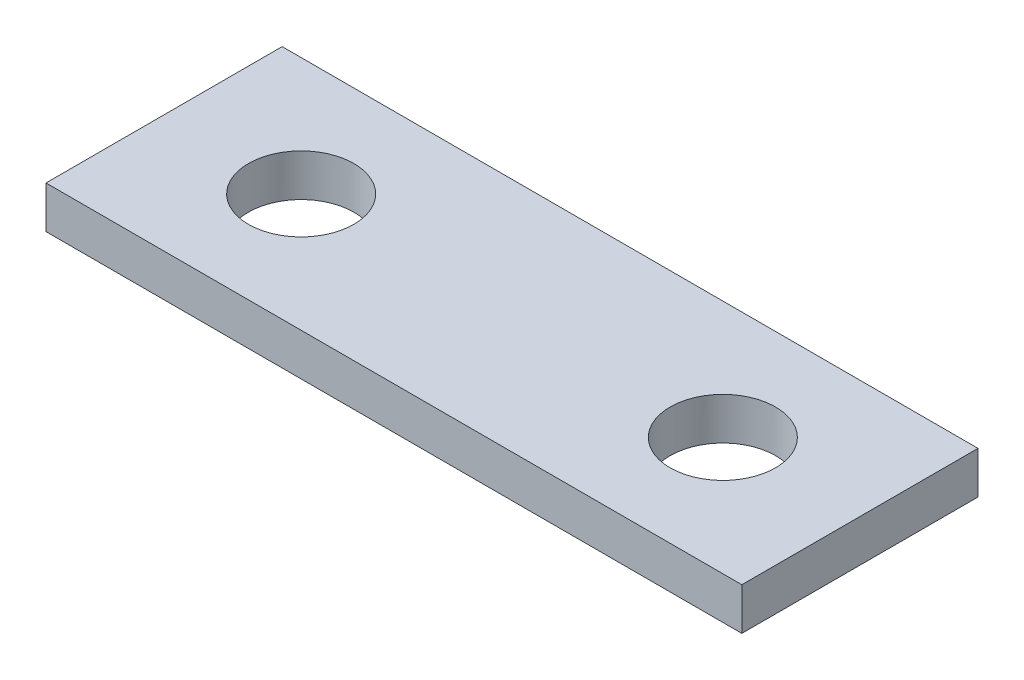
SolidWorks part; units mm, degrees
material "1060 Alloy"
ref_plane "Front Plane" through (0, 0, 0) normal (0, 0, 1) x (1, 0, 0)
ref_plane "Top Plane" through (0, 0, 0) normal (0, 1, 0) x (1, 0, 0)
ref_plane "Right Plane" through (0, 0, 0) normal (1, 0, 0) x (0, 0, -1)
sketch "Sketch1" plane through (0, 0, 0) normal (0, 1, 0) x (1, 0, 0)
  line L1 (0, 0) -> (16.5, 0)
  line L2 (0, 0) -> (0, 5.6)
  line L3 (0, 5.6) -> (16.5, 5.6)
  line L4 (16.5, 0) -> (16.5, 5.6)
  dimension "D1" = 16.5
  dimension "D2" = 5.6
extrude "Boss-Extrude1" add sketch "Sketch1" along normal blind 1
hole_wizard "M3x0.5 Tapped Hole3" positions "Sketch7" profile "Sketch8" tap size "M3x0.5" standard "Ansi Metric" end condition up to next
sketch "Sketch7" plane through (0, 1, 0) normal (0, 1, 0) x (-1, 0, 0)
  line L0 (0, -2.8) -> (-16.5, -2.8) construction
  line L1 (0, -5.6) -> (0, 0) construction
  line L2 (-16.5, 0) -> (-16.5, -5.6) construction
  point P0 (-3.25, -2.8)
  point P1 (-13.25, -2.8)
  point P19 (-16.5, -2.74)
  dimension "D1" = 10
  dimension "D2" = 3.25
sketch "Sketch8" plane through (3.25, 1, -2.8) normal (1, 0, 0) x (0, 0, 1)
  line L0 (0, 0) -> (0, 1)
  line L1 (0, 1) -> (1.25, 1)
  line L2 (1.25, 1) -> (1.25, 0)
  line L5 (1.25, 0) -> (0, 0)
  line L11 (0, -6.35) -> (0, 107.95) construction
  dimension "Thru Tap Drill Dia." = 2.5
  dimension "Thru Tap Drill Depth" = 1
cosmetic thread "Hole Thread5" parameters "D2"=3
cosmetic thread "Hole Thread6" parameters "D2"=3
